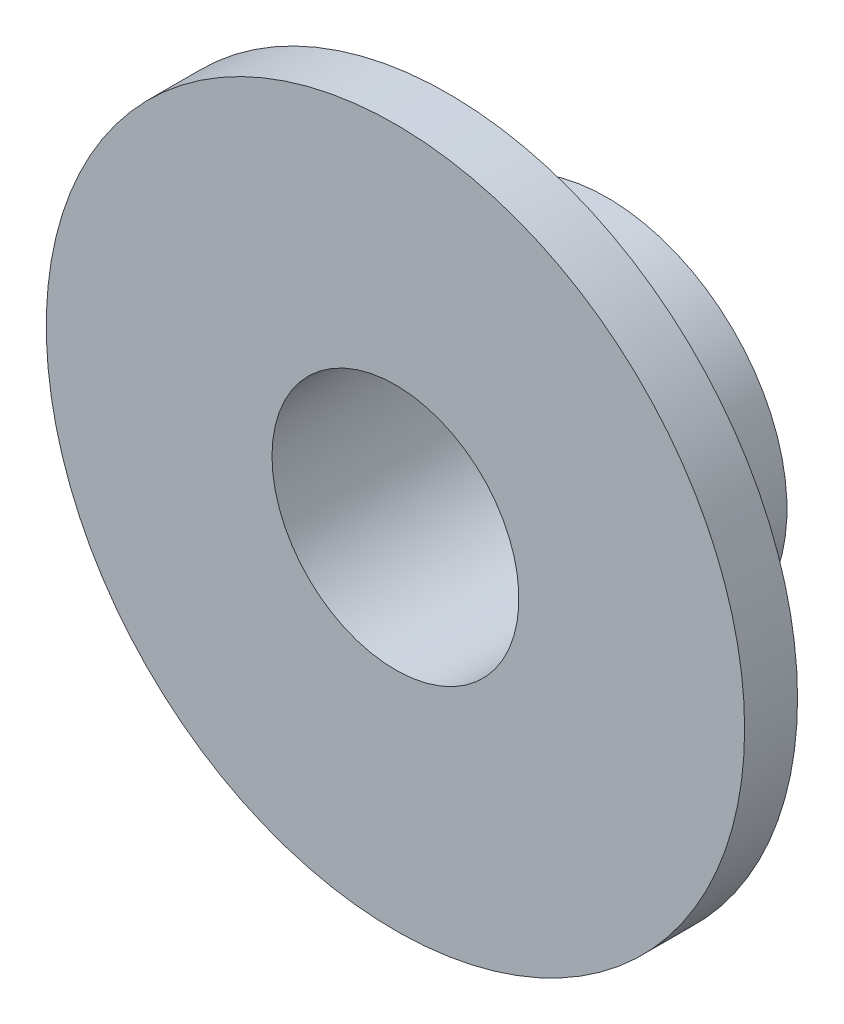
SolidWorks part; units mm, degrees
ref_plane "Front Plane" through (0, 0, 0) normal (0, 0, 1) x (1, 0, 0)
ref_plane "Top Plane" through (0, 0, 0) normal (0, 1, 0) x (1, 0, 0)
ref_plane "Right Plane" through (0, 0, 0) normal (1, 0, 0) x (0, 0, -1)
sketch "Sketch1" plane through (0, 0, 28.9638) normal (0, 0, 1) x (1, 0, 0)
  circle A0 centre (13.758, 17.3841) radius 9.9
  dimension "D1" = 19.8
extrude "Boss-Extrude1" add sketch "Sketch1" along normal blind 1.5
sketch "Sketch2" plane through (0, 0, 28.9638) normal (0, 0, -1) x (-1, 0, 0)
  circle A0 centre (-13.758, 17.3841) radius 5.1
  dimension "D1" = 10.2
extrude "Boss-Extrude2" add sketch "Sketch2" along normal blind 4.5
sketch "Sketch3" plane through (0, 0, 24.4638) normal (0, 0, -1) x (-1, 0, 0)
  circle A0 centre (-13.758, 17.3841) radius 3.5
  dimension "D1" = 7
extrude "Cut-Extrude1" cut sketch "Sketch3" against normal through all
